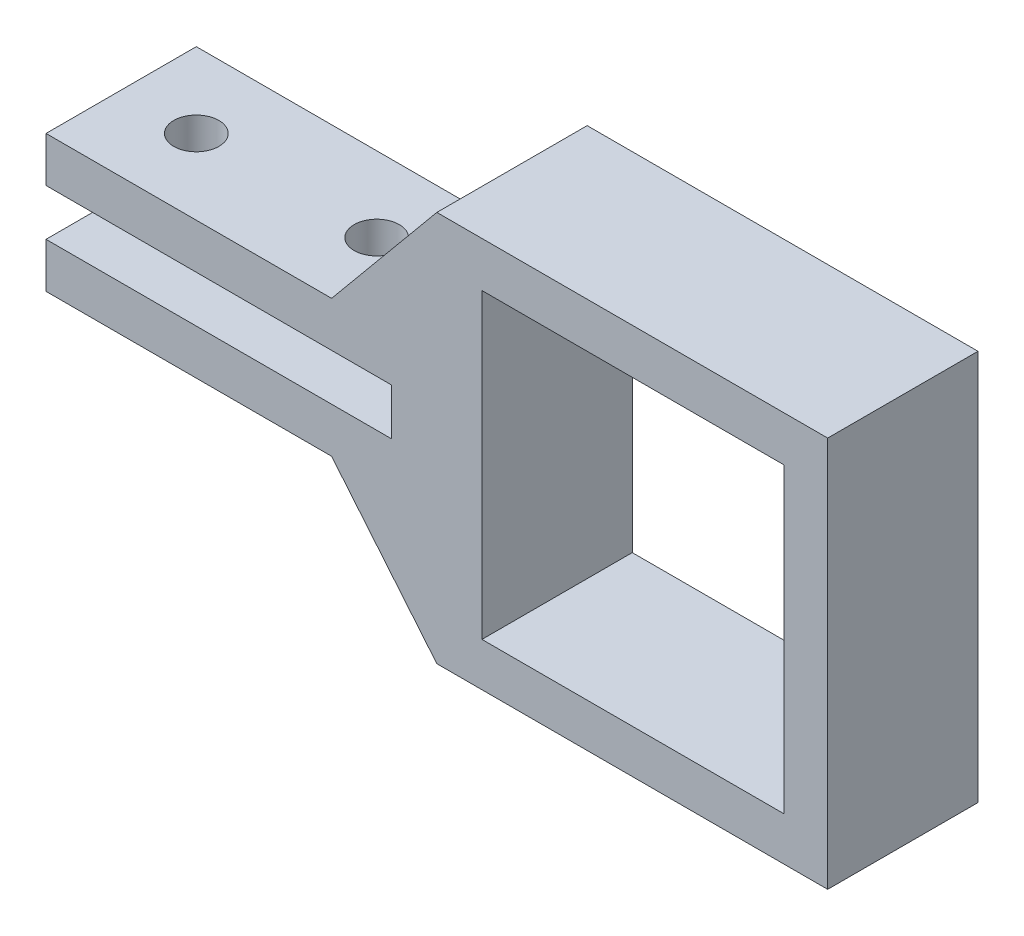
SolidWorks part; units mm, degrees
ref_plane "前视基准面" through (0, 0, 0) normal (0, 0, 1) x (1, 0, 0)
ref_plane "上视基准面" through (0, 0, 0) normal (0, 1, 0) x (1, 0, 0)
ref_plane "右视基准面" through (0, 0, 0) normal (1, 0, 0) x (0, 0, -1)
sketch "草图1" plane through (0, 0, 0) normal (0, 0, 1) x (1, 0, 0)
  line L68 (-21.1315, 0) -> (10.2214, 0) construction
  line L78 (-26, 4.55) -> (-26, 1.55)
  line L79 (-26, 4.55) -> (-7, 4.55)
  line L82 (-26, 1.55) -> (-3, 1.55)
  line L83 (0, 4.55) -> (0, 13) construction
  line L84 (0, 13) -> (26, 13)
  line L85 (0, -13) -> (26, -13)
  line L86 (0, -4.55) -> (0, -13) construction
  line L87 (-26, -1.55) -> (-3, -1.55)
  line L90 (-26, -4.55) -> (-7, -4.55)
  line L91 (-26, -4.55) -> (-26, -1.55)
  line L92 (-3, 1.55) -> (-3, -1.55)
  line L93 (26, 13) -> (26, -13)
  line L94 (0, 1.55) -> (0, 4.55) construction
  line L95 (0, -1.55) -> (0, -4.55) construction
  line L96 (0, -13) -> (-7, -4.55)
  line L97 (0, 13) -> (-7, 4.55)
  line L98 (-7, 4.55) -> (0, 4.55) construction
  line L99 (-7, -4.55) -> (0, -4.55) construction
  dimension "D1" = 26
  dimension "D2" = 26
  dimension "D3" = 3.1
  dimension "D4" = 23
  dimension "D5" = 7
  dimension "D6" = 7
  dimension "D8" = 26
  dimension "5" = 3
extrude "凸台-拉伸1" add sketch "草图1" along normal blind 10 contours L85 L93 L84 L97 L79 L78 L82 L92 L87 L91 L90 L96
sketch "草图5" plane through (0, 0, 10) normal (0, 0, 1) x (1, 0, 0)
  line L0 (3, 10) -> (3, -10.1)
  line L1 (3, -10.1) -> (23.1, -10.1)
  line L3 (23.1, 10) -> (3, 10)
  line L17 (23.1, 10) -> (23.1, -10.1)
  dimension "D1" = 20.1
  dimension "D2" = 20.1
extrude "切除-拉伸1" cut sketch "草图5" against normal blind 30
sketch "草图7" plane through (0, 4.55, 0) normal (0, 1, 0) x (1, 0, 0)
  line L0 (-21, -5) -> (-26, -5) construction
  line L2 (-26, -10) -> (-26, 0) construction
  line L3 (-21, -5) -> (-21, 0) construction
  line L4 (-26, 0) -> (-7, 0) construction
  circle A0 centre (-21, -5) radius 1.5
  circle A1 centre (-9, -5) radius 1.5
  dimension "D1" = 3
  dimension "D2" = 5
  dimension "D3" = 5
  dimension "D5" = 12
  dimension "D4" = 2
extrude "切除-拉伸5" cut sketch "草图7" against normal up to surface (9.1 mm away) up to face at (-16.5, -4.55, 5)
